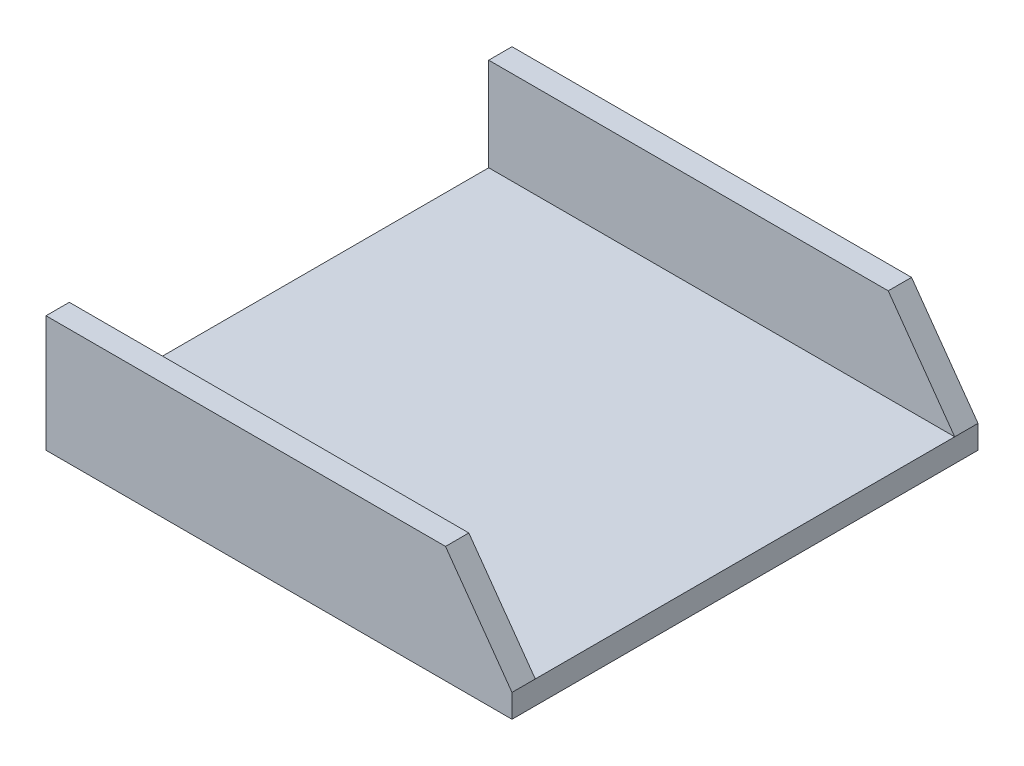
SolidWorks part; units mm, degrees
other "Markup1"
sketch "Sketch2" plane through (600, 150, 0) normal (0.275, 0.8562, 0.4373) x (0.8465, 0, -0.5323)
material "Gray Cast Iron"
ref_plane "Front Plane" through (0, 0, 0) normal (0, 0, 1) x (1, 0, 0)
ref_plane "Top Plane" through (0, 0, 0) normal (0, 1, 0) x (1, 0, 0)
ref_plane "Right Plane" through (0, 0, 0) normal (1, 0, 0) x (0, 0, -1)
sketch "Sketch1" plane through (0, 0, 0) normal (1, 0, 0) x (0, 0, -1)
  line L0 (30, 150) -> (30, 30)
  line L1 (0, 0) -> (600, 0)
  line L2 (0, 0) -> (0, 150)
  line L3 (0, 150) -> (30, 150)
  line L4 (600, 0) -> (600, 150)
  line L5 (30, 30) -> (570, 30)
  line L6 (570, 30) -> (570, 150)
  line L7 (570, 150) -> (600, 150)
  point P7 (570.3961, 150)
  dimension "D1" = 600
  dimension "D2" = 150
  dimension "D3" = 30
  dimension "D4" = 30
  dimension "D5" = 30
extrude "Boss-Extrude1" add sketch "Sketch1" along normal blind 600
sketch "Sketch4" plane through (0, 0, -30) normal (0, 0, -1) x (-1, 0, 0)
  line L0 (-600, 30) -> (-514.4101, 150)
  line L1 (-600, 150) -> (0, 150) construction
  line L2 (-514.4101, 150) -> (-600, 150)
  line L3 (-600, 150) -> (-600, 30)
  point P5 (-602.3424, 30)
extrude "Cut-Extrude1" cut sketch "Sketch4" against normal blind 600 and the other way blind 600
